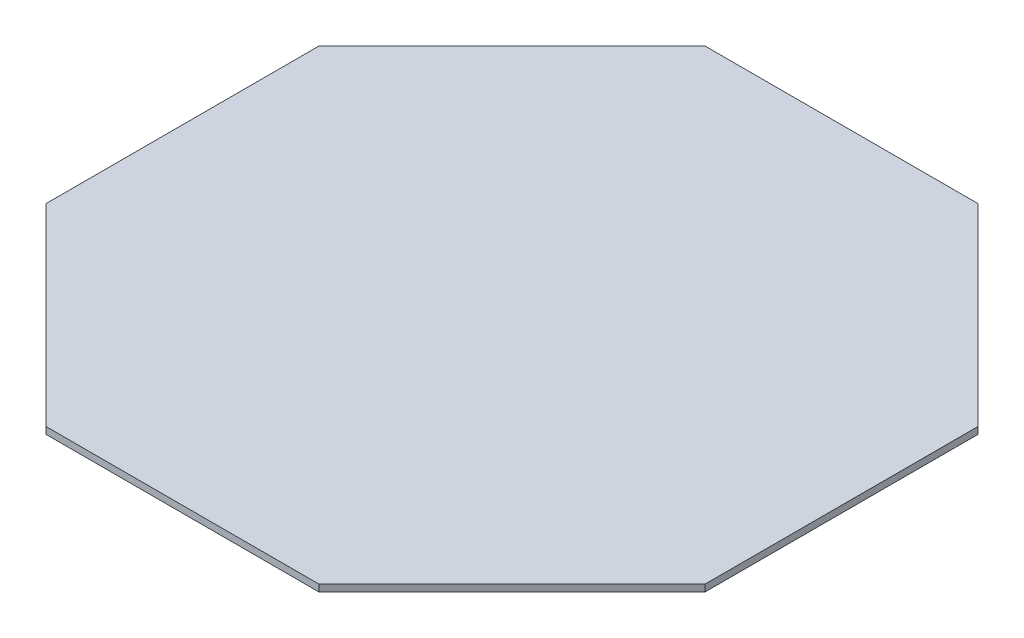
SolidWorks part; units mm, degrees
ref_plane "Plan de face" through (0, 0, 0) normal (0, 0, 1) x (1, 0, 0)
ref_plane "Plan de dessus" through (0, 0, 0) normal (0, 1, 0) x (1, 0, 0)
ref_plane "Plan de droite" through (0, 0, 0) normal (1, 0, 0) x (0, 0, -1)
sketch "Esquisse1" plane through (0, 0, 0) normal (0, 1, 0) x (1, 0, 0)
  line L0 (0, 0) -> (144.8528, 0) construction
  line L1 (144.8528, 60) -> (60, 144.8528)
  line L2 (60, 144.8528) -> (-60, 144.8528)
  line L3 (-60, 144.8528) -> (-144.8528, 60)
  line L4 (-144.8528, 60) -> (-144.8528, -60)
  line L5 (-144.8528, -60) -> (-60, -144.8528)
  line L6 (-60, -144.8528) -> (60, -144.8528)
  line L7 (60, -144.8528) -> (144.8528, -60)
  line L8 (144.8528, -60) -> (144.8528, 60)
  line L9 (0, 144.8528) -> (0, -144.8528) construction
  line L10 (-144.8528, 0) -> (0, 0) construction
  circle A0 centre (0, 0) radius 144.8528 construction
  dimension "D1" = 120
extrude "Extrusion1" add sketch "Esquisse1" along normal blind 3
